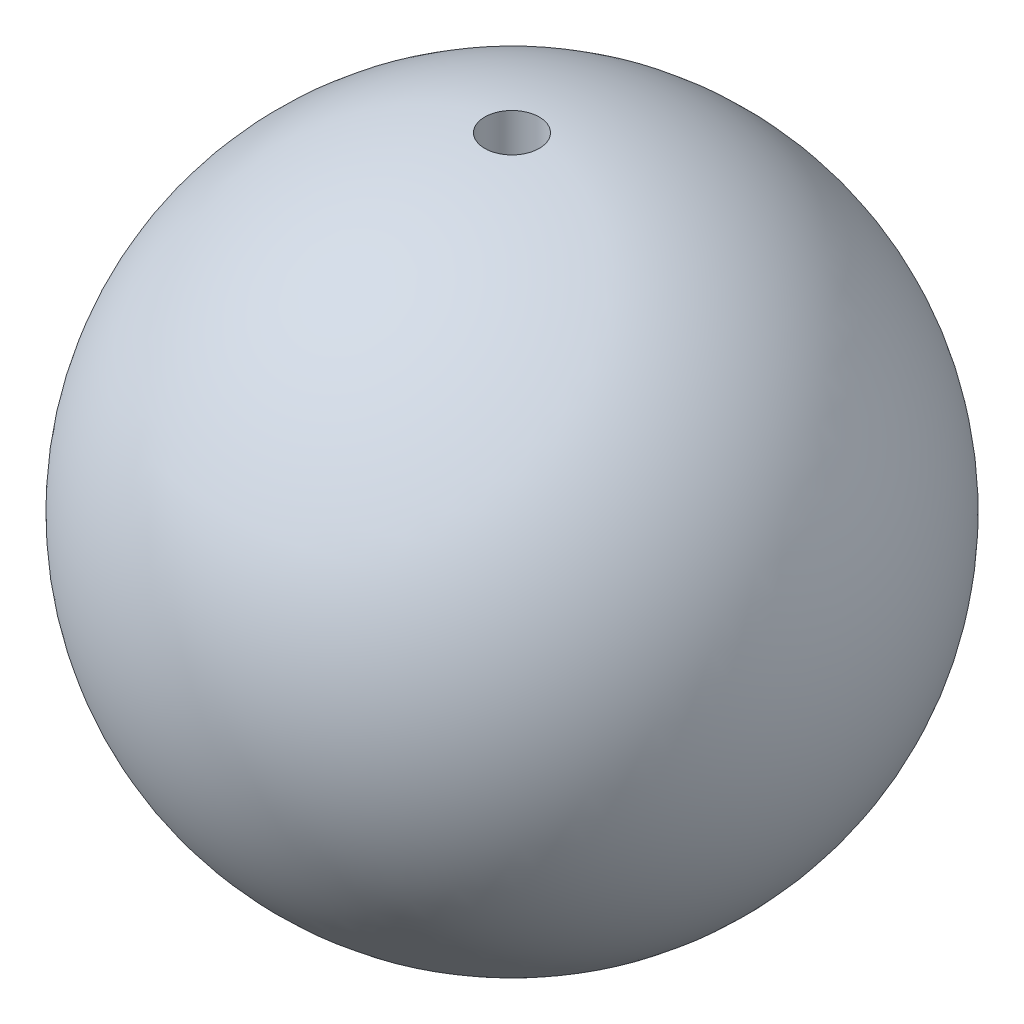
SolidWorks part; units mm, degrees
material "Pure Lead"
ref_plane "Front Plane" through (0, 0, 0) normal (0, 0, 1) x (1, 0, 0)
ref_plane "Top Plane" through (0, 0, 0) normal (0, 1, 0) x (1, 0, 0)
ref_plane "Right Plane" through (0, 0, 0) normal (1, 0, 0) x (0, 0, -1)
sketch "Sketch1" plane through (0, 0, 0) normal (0, 0, 1) x (1, 0, 0)
  line L0 (0, 19.05) -> (0, -19.05) construction
  line L1 (0, 19.05) -> (0, -19.05)
  arc A0 (0, -19.05) -> (0, 19.05) centre (0, 0) ccw
  dimension "D1" = 38.1
revolve "Revolve1" add sketch "Sketch1" angle 360 about L0
sketch "Sketch2" plane through (0, 0, 0) normal (0, 1, 0) x (1, 0, 0)
  circle A0 centre (0, 0) radius 1.5748
  dimension "D1" = 3.1496
extrude "Hole" cut sketch "Sketch2" along normal through all
